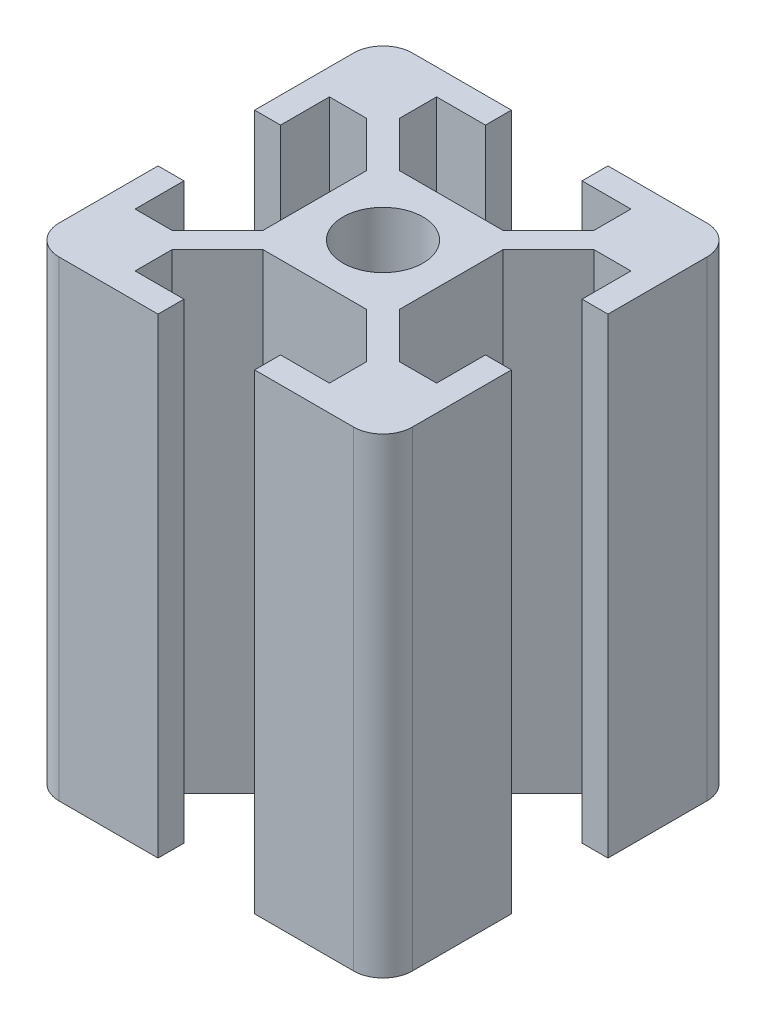
SolidWorks part; units mm, degrees
ref_plane "Front Plane" through (0, 0, 0) normal (0, 0, 1) x (1, 0, 0)
ref_plane "Top Plane" through (0, 0, 0) normal (0, 1, 0) x (1, 0, 0)
ref_plane "Right Plane" through (0, 0, 0) normal (1, 0, 0) x (0, 0, -1)
sketch "Sketch1" plane through (0, 0, 0) normal (0, 1, 0) x (1, 0, 0)
  line L0 (5.8, 4.3858) -> (5.8, -4.3858)
  line L1 (-12.5, 15) -> (-4.1, 15)
  line L2 (-15, 12.5) -> (-15, 4.1)
  line L3 (-12.5, -15) -> (-4.1, -15)
  line L4 (15, 12.5) -> (15, 4.1)
  line L5 (-15, 15) -> (15, -15) construction
  line L6 (-15, -15) -> (15, 15) construction
  line L7 (-5.8, 4.3858) -> (-5.8, -4.3858)
  line L8 (-4.3858, 5.8) -> (4.3858, 5.8)
  line L9 (-4.3858, -5.8) -> (4.3858, -5.8)
  line L10 (-8.25, -9.6642) -> (-4.3858, -5.8)
  line L11 (-9.6642, 8.25) -> (-5.8, 4.3858)
  line L12 (-9.6642, -8.25) -> (-5.8, -4.3858)
  line L13 (-8.25, 9.6642) -> (-4.3858, 5.8)
  line L14 (-8.25, 12.8) -> (-8.25, 9.6642)
  line L15 (-12.8, 8.25) -> (-9.6642, 8.25)
  line L16 (8.25, 12.8) -> (8.25, 9.6642)
  line L17 (9.6642, 8.25) -> (12.8, 8.25)
  line L18 (-12.8, -8.25) -> (-9.6642, -8.25)
  line L19 (-8.25, -9.6642) -> (-8.25, -12.8)
  line L20 (8.25, -9.6642) -> (8.25, -12.8)
  line L21 (9.6642, -8.25) -> (12.8, -8.25)
  line L22 (-14.2929, 15.7071) -> (15.7071, -14.2929) construction
  line L23 (-15.7071, 14.2929) -> (14.2929, -15.7071) construction
  line L24 (-12.8, 8.25) -> (-12.8, 4.1)
  line L25 (-15.7071, -14.2929) -> (14.2929, 15.7071) construction
  line L26 (12.8, 8.25) -> (12.8, 4.1)
  line L27 (-14.2929, -15.7071) -> (15.7071, 14.2929) construction
  line L28 (-8.25, -12.8) -> (-4.1, -12.8)
  line L29 (-8.25, 12.8) -> (-4.1, 12.8)
  line L30 (-15, -4.1) -> (-12.8, -4.1)
  line L31 (-15, 4.1) -> (-12.8, 4.1)
  line L32 (-4.1, 12.8) -> (-4.1, 15)
  line L33 (4.1, 15) -> (4.1, 12.8)
  line L34 (15, -4.1) -> (12.8, -4.1)
  line L35 (12.8, 4.1) -> (15, 4.1)
  line L36 (-4.1, -12.8) -> (-4.1, -15)
  line L37 (4.1, -12.8) -> (4.1, -15)
  line L38 (12.8, -4.1) -> (12.8, -8.25)
  line L39 (4.1, -12.8) -> (8.25, -12.8)
  line L40 (-12.8, -4.1) -> (-12.8, -8.25)
  line L41 (4.1, 12.8) -> (8.25, 12.8)
  line L42 (5.8, 4.3858) -> (9.6642, 8.25)
  line L43 (4.3858, 5.8) -> (8.25, 9.6642)
  line L48 (4.3858, -5.8) -> (8.25, -9.6642)
  line L49 (5.8, -4.3858) -> (9.6642, -8.25)
  line L50 (15, -4.1) -> (15, -12.5)
  line L51 (4.1, -15) -> (12.5, -15)
  line L52 (-15, -4.1) -> (-15, -12.5)
  line L53 (4.1, 15) -> (12.5, 15)
  circle A0 centre (0, 0) radius 3.4
  arc A1 (-12.5, 15) -> (-15, 12.5) centre (-12.5, 12.5) ccw
  arc A2 (-15, -12.5) -> (-12.5, -15) centre (-12.5, -12.5) ccw
  arc A3 (12.5, -15) -> (15, -12.5) centre (12.5, -12.5) ccw
  arc A4 (12.5, 15) -> (15, 12.5) centre (12.5, 12.5) cw
  point P0 (0, 0)
  point P22 (5.8, 0)
  point P24 (0, 5.8)
  point P26 (-5.8, 0)
  point P29 (0, -5.8)
  dimension "D30" = 6.8
  dimension "D31" = 2.5
  dimension "D1" = 30
  dimension "D2" = 30
  dimension "D3" = 9.2
  dimension "D4" = 9.2
  dimension "D5" = 9.2
  dimension "D6" = 9.2
  dimension "D7" = 1
  dimension "D9" = 16.5
  dimension "D10" = 4.1
  dimension "D11" = 16.5
  dimension "D12" = 4.1
  dimension "D13" = 16.5
  dimension "D14" = 8.25
  dimension "D15" = 16.5
  dimension "D16" = 4.1
  dimension "D17" = 2.2
  dimension "D18" = 2.2
  dimension "D19" = 2.2
  dimension "D20" = 2.2
  dimension "D21" = 8.2
  dimension "D22" = 8.25
  dimension "D23" = 8.2
  dimension "D24" = 8.25
  dimension "D25" = 8.2
  dimension "D26" = 8.25
  dimension "D27" = 8.2
  dimension "D28" = 4.1
  dimension "D29" = 2
  dimension "D8" = 1
extrude "Boss-Extrude1" add sketch "Sketch1" along normal blind 40
